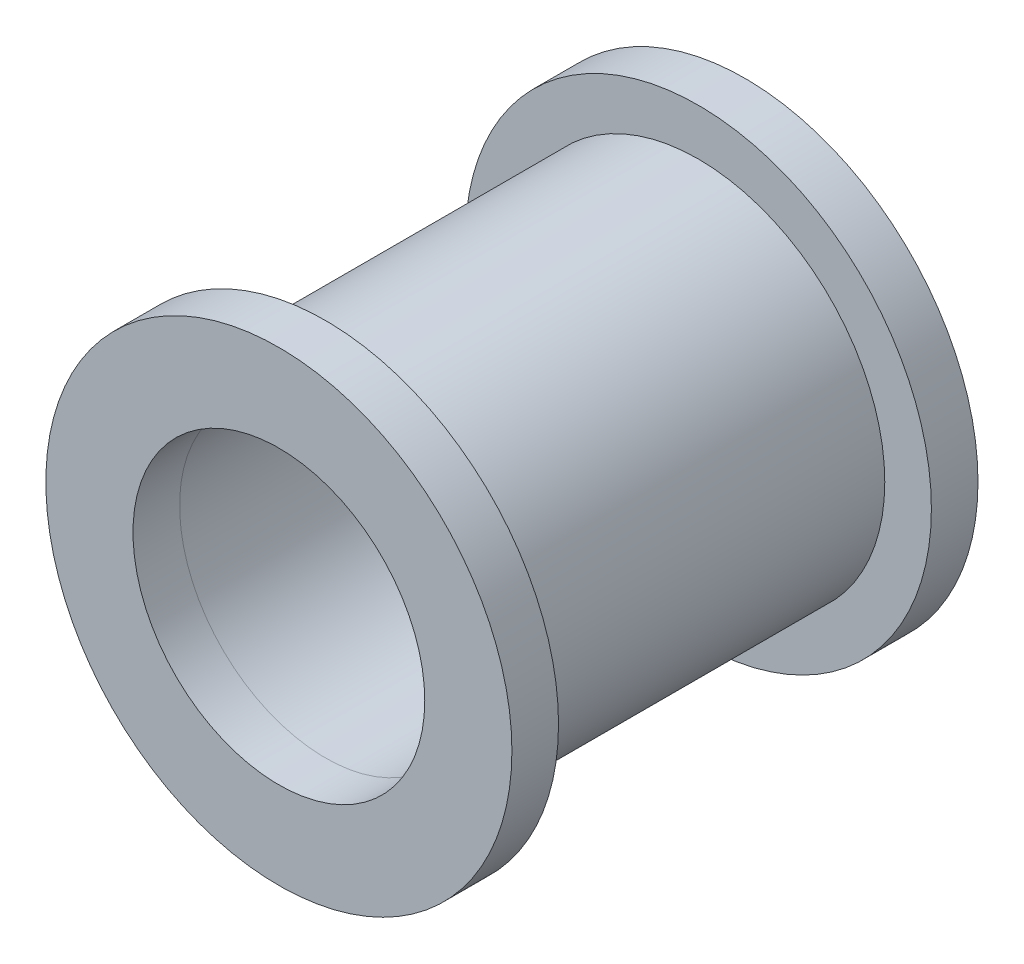
SolidWorks part; units mm, degrees
ref_plane "Front Plane" through (0, 0, 0) normal (0, 0, 1) x (1, 0, 0)
ref_plane "Top Plane" through (0, 0, 0) normal (0, 1, 0) x (1, 0, 0)
ref_plane "Right Plane" through (0, 0, 0) normal (1, 0, 0) x (0, 0, -1)
sketch "Sketch1" plane through (0, 0, 0) normal (0, 0, 1) x (1, 0, 0)
  circle A0 centre (0, 0) radius 5.08
  circle A1 centre (0, 0) radius 3.9751
  dimension "D1" = 10.16
  dimension "D2" = 7.9502
extrude "Boss-Extrude1" add sketch "Sketch1" against normal blind 5.08
sketch "Sketch2" plane through (0, 0, 0) normal (0, 0, 1) x (1, 0, 0)
  circle A0 centre (0, 0) radius 6.35
  circle A2 centre (0, 0) radius 3.9751
  dimension "D1" = 12.7
extrude "Boss-Extrude2" add sketch "Sketch2" along normal blind 1.27 separate body
mirror "Mirror1" about plane through (0, 0, -5.08) normal (0, 0, 1) of "Boss-Extrude2", "Boss-Extrude1"
